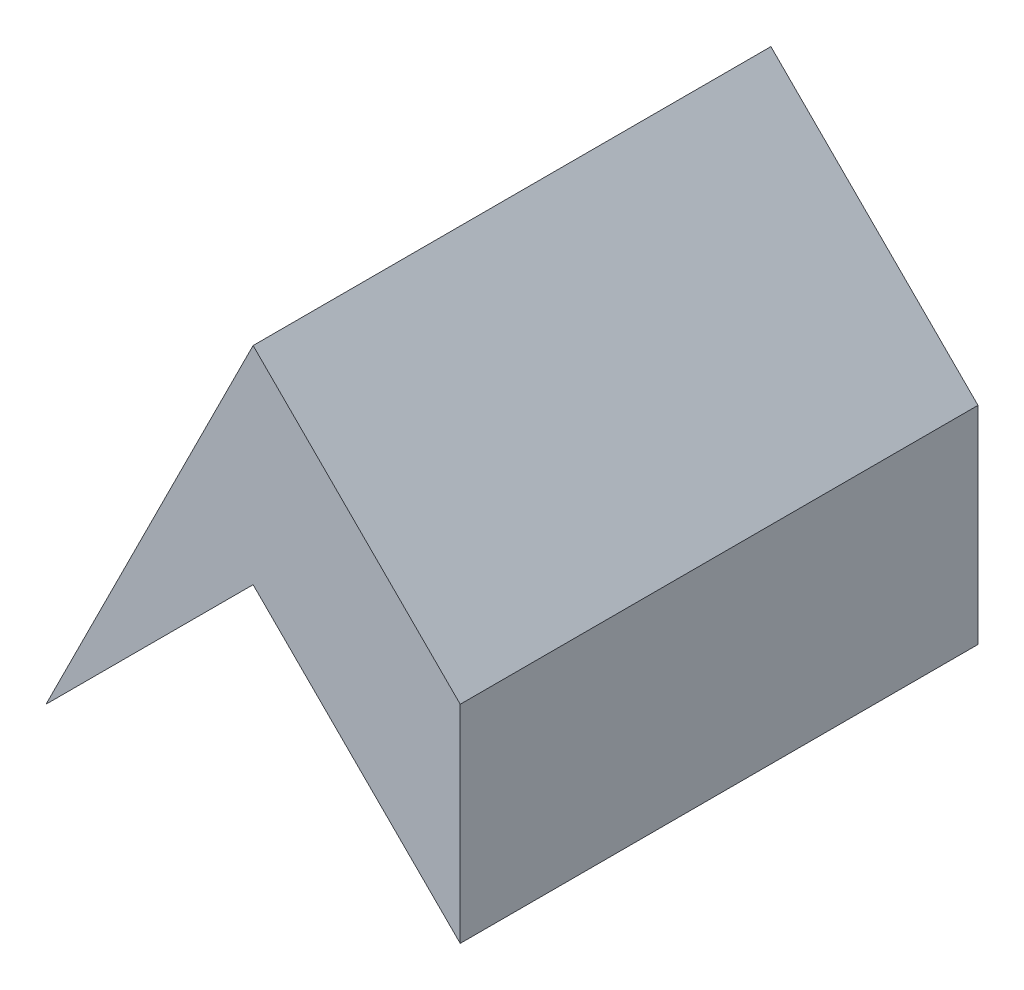
SolidWorks part; units mm, degrees
ref_plane "Front Plane" through (0, 0, 0) normal (0, 0, 1) x (1, 0, 0)
ref_plane "Top Plane" through (0, 0, 0) normal (0, 1, 0) x (1, 0, 0)
ref_plane "Right Plane" through (0, 0, 0) normal (1, 0, 0) x (0, 0, -1)
sketch "Sketch1" plane through (0, 0, 0) normal (0, 0, 1) x (1, 0, 0)
  line L0 (-20, 0) -> (-10, 20)
  line L1 (-10, 20) -> (0, 10)
  line L2 (0, 10) -> (0, 0)
  line L3 (0, 0) -> (-10, 10)
  line L4 (-10, 10) -> (-20, 0)
  point P2 (-10, 0)
  dimension "D1" = 10
  dimension "D2" = 10
  dimension "D3" = 10
extrude "Boss-Extrude1" add sketch "Sketch1" along normal blind 25
